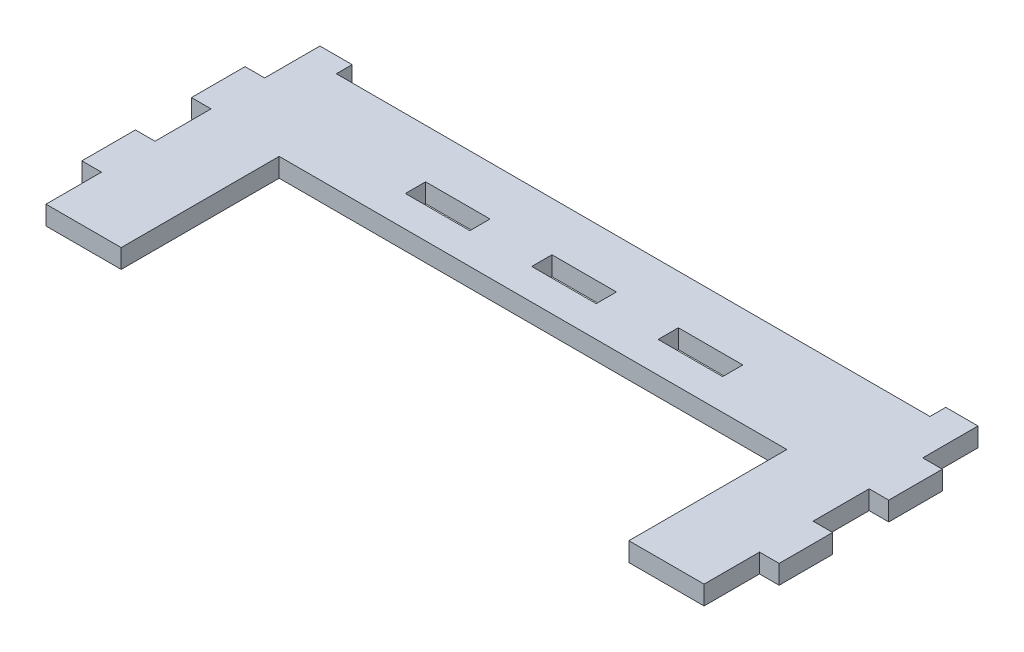
SolidWorks part; units mm, degrees
ref_plane "Front Plane" through (0, 0, 0) normal (0, 0, 1) x (1, 0, 0)
ref_plane "Top Plane" through (0, 0, 0) normal (0, 1, 0) x (1, 0, 0)
ref_plane "Right Plane" through (0, 0, 0) normal (1, 0, 0) x (0, 0, -1)
sketch "Sketch1" plane through (0, 0, 0) normal (0, 1, 0) x (1, 0, 0)
  line L0 (0, 0) -> (0, 52.05) construction
  line L1 (-55.1722, 52.05) -> (55.1722, 52.05) construction
  line L2 (-55.1722, 52.05) -> (-55.1722, 0) construction
  line L3 (-55.1722, 0) -> (55.1722, 0) construction
  line L4 (55.1722, 52.05) -> (55.1722, 0) construction
  line L5 (-40.1722, 0) -> (-40.1722, 30) construction
  line L6 (-55.1722, 30) -> (55.1722, 30) construction
  line L7 (40.1722, 30) -> (40.1722, 0) construction
  line L8 (-40.1722, 0) -> (-55.1722, 0)
  line L9 (40.1722, 0) -> (55.1722, 0)
  line L10 (-55.1722, 33) -> (55.1722, 33) construction
  line L11 (-55.1722, 43.95) -> (55.1722, 43.95)
  line L12 (-40.1722, 30) -> (-43.1722, 30) construction
  line L13 (-43.1722, 40.95) -> (43.1722, 40.95) construction
  line L14 (-40.1722, 25) -> (40.1722, 25)
  line L15 (-43.1722, 30) -> (-43.1722, 43.95) construction
  line L16 (-43.1722, 43.95) -> (-55.1722, 43.95) construction
  line L17 (-55.1722, 43.95) -> (-55.1722, 0)
  line L18 (40.1722, 30) -> (43.1722, 30) construction
  line L19 (43.1722, 30) -> (43.1722, 43.95) construction
  line L20 (43.1722, 43.95) -> (55.1722, 43.95) construction
  line L21 (55.1722, 43.95) -> (55.1722, 0)
  line L22 (40.1722, 25) -> (40.1722, 0)
  line L23 (-40.1722, 0) -> (-40.1722, 25)
  dimension "D1" = 15
  dimension "D2" = 12
extrude "Boss-Extrude1" add sketch "Sketch1" against normal up to vertex (3 mm away) contours L16 L17 L8 L5 L12 L15 | L21 L20 L19 L18 L7 L9
sketch "Sketch2" plane through (0, 0, 0) normal (0, 1, 0) x (1, 0, 0)
  line L0 (-52.0722, 43.475) -> (-52.0722, 34.6) construction
  line L1 (-55.2722, 34.6) -> (-52.0722, 34.6) construction
  line L2 (-55.2722, 43.475) -> (-55.2722, 34.6) construction
  line L3 (-55.2722, 43.475) -> (-52.0722, 43.475) construction
  line L4 (-52.0722, 26.125) -> (-52.0722, 17.25) construction
  line L5 (-55.2722, 17.25) -> (-52.0722, 17.25) construction
  line L6 (-55.2722, 26.125) -> (-55.2722, 17.25) construction
  line L7 (-55.2722, 26.125) -> (-52.0722, 26.125) construction
  line L8 (-52.0722, 8.775) -> (-52.0722, -0.1) construction
  line L9 (-55.2722, -0.1) -> (-52.0722, -0.1) construction
  line L10 (-55.2722, 8.775) -> (-55.2722, -0.1) construction
  line L11 (-55.2722, 8.775) -> (-52.0722, 8.775) construction
  line L12 (-46.9722, 40.85) -> (46.9722, 40.85)
  line L13 (55.2722, 44.05) -> (-55.2722, 44.05)
  line L16 (-36.7722, 44.05) -> (-36.7722, 40.85) construction
  line L17 (-46.9722, 40.85) -> (-36.7722, 40.85) construction
  line L18 (-46.9722, 43.35) -> (-46.9722, 40.85)
  line L19 (-52.0722, 43.35) -> (-46.9722, 43.35)
  line L20 (-46.9722, 44.05) -> (-36.7722, 44.05) construction
  line L21 (-36.7722, 44.05) -> (-36.7722, 40.85) construction
  line L22 (-46.9722, 40.85) -> (-36.7722, 40.85) construction
  line L23 (-46.9722, 44.05) -> (-46.9722, 40.85) construction
  line L24 (-52.0722, 34.6) -> (-52.0722, 43.35)
  line L25 (-55.2722, 34.6) -> (-52.0722, 34.6)
  line L26 (-55.2722, 44.05) -> (-55.2722, 34.6)
  line L27 (-36.7722, 44.05) -> (-55.2722, 44.05) construction
  line L28 (-52.0722, 43.475) -> (-52.0722, 34.6) construction
  line L29 (-55.2722, 34.6) -> (-52.0722, 34.6) construction
  line L30 (-55.2722, 43.475) -> (-55.2722, 34.6) construction
  line L31 (-55.2722, 43.475) -> (-52.0722, 43.475) construction
  line L32 (-52.0722, 26.125) -> (-52.0722, 17.25)
  line L33 (-55.2722, 17.25) -> (-52.0722, 17.25)
  line L34 (-55.2722, 26.125) -> (-55.2722, 17.25)
  line L35 (-55.2722, 26.125) -> (-52.0722, 26.125)
  line L36 (-52.0722, 8.775) -> (-52.0722, -0.1)
  line L37 (-55.2722, -0.1) -> (-52.0722, -0.1)
  line L38 (-55.2722, 8.775) -> (-55.2722, -0.1)
  line L39 (-55.2722, 8.775) -> (-52.0722, 8.775)
  line L40 (0, 0) -> (0, 44.05) construction
  line L41 (55.2722, 8.775) -> (52.0722, 8.775)
  line L42 (55.2722, 8.775) -> (55.2722, -0.1)
  line L43 (55.2722, -0.1) -> (52.0722, -0.1)
  line L44 (52.0722, 8.775) -> (52.0722, -0.1)
  line L45 (55.2722, 26.125) -> (52.0722, 26.125)
  line L46 (55.2722, 26.125) -> (55.2722, 17.25)
  line L47 (55.2722, 17.25) -> (52.0722, 17.25)
  line L48 (-46.9722, 44.05) -> (-36.7722, 44.05) construction
  line L49 (-36.7722, 44.05) -> (-36.7722, 40.85) construction
  line L50 (-46.9722, 40.85) -> (-36.7722, 40.85) construction
  line L51 (-46.9722, 44.05) -> (-46.9722, 40.85) construction
  line L52 (52.0722, 26.125) -> (52.0722, 17.25)
  line L53 (46.9722, 44.05) -> (46.9722, 40.85) construction
  line L54 (46.9722, 44.05) -> (36.7722, 44.05) construction
  line L55 (36.7722, 44.05) -> (36.7722, 40.85) construction
  line L56 (46.9722, 40.85) -> (36.7722, 40.85) construction
  line L57 (55.2722, 43.475) -> (52.0722, 43.475) construction
  line L58 (55.2722, 43.475) -> (55.2722, 34.6) construction
  line L59 (55.2722, 34.6) -> (52.0722, 34.6)
  line L60 (52.0722, 43.475) -> (52.0722, 34.6) construction
  line L61 (36.7722, 44.05) -> (55.2722, 44.05) construction
  line L62 (55.2722, 44.05) -> (55.2722, 34.6)
  line L63 (52.0722, 34.6) -> (52.0722, 43.35)
  line L75 (53.6722, 44.05) -> (53.6722, 43.475) construction
  line L78 (52.0722, 43.35) -> (46.9722, 43.35)
  line L79 (46.9722, 43.35) -> (46.9722, 40.85)
  line L80 (-25.1, 33.1) -> (-14.9, 33.1) construction
  line L81 (-14.9, 33.1) -> (-14.9, 29.9) construction
  line L82 (-25.1, 29.9) -> (-14.9, 29.9) construction
  line L83 (-25.1, 33.1) -> (-25.1, 29.9) construction
  line L85 (25.1, 33.1) -> (14.9, 33.1) construction
  line L86 (14.9, 33.1) -> (14.9, 29.9) construction
  line L87 (25.1, 29.9) -> (14.9, 29.9) construction
  line L88 (25.1, 33.1) -> (25.1, 29.9) construction
  line L89 (-25.1, 33.1) -> (-14.9, 33.1)
  line L90 (-14.9, 33.1) -> (-14.9, 29.9)
  line L91 (-25.1, 29.9) -> (-14.9, 29.9)
  line L92 (-25.1, 33.1) -> (-25.1, 29.9)
  line L93 (5.1, 33.1) -> (-5.1, 33.1) construction
  line L94 (25.1, 33.1) -> (14.9, 33.1)
  line L95 (14.9, 33.1) -> (14.9, 29.9)
  line L96 (25.1, 29.9) -> (14.9, 29.9)
  line L97 (25.1, 33.1) -> (25.1, 29.9)
  line L98 (-5.1, 33.1) -> (-5.1, 29.9) construction
  line L99 (5.1, 29.9) -> (-5.1, 29.9) construction
  line L100 (5.1, 33.1) -> (5.1, 29.9) construction
  line L101 (5.1, 33.1) -> (-5.1, 33.1)
  line L102 (-5.1, 33.1) -> (-5.1, 29.9)
  line L103 (5.1, 29.9) -> (-5.1, 29.9)
  line L104 (5.1, 33.1) -> (5.1, 29.9)
  dimension "D1" = 0.7
extrude "Cut-Extrude1" cut sketch "Sketch2" against normal through all
